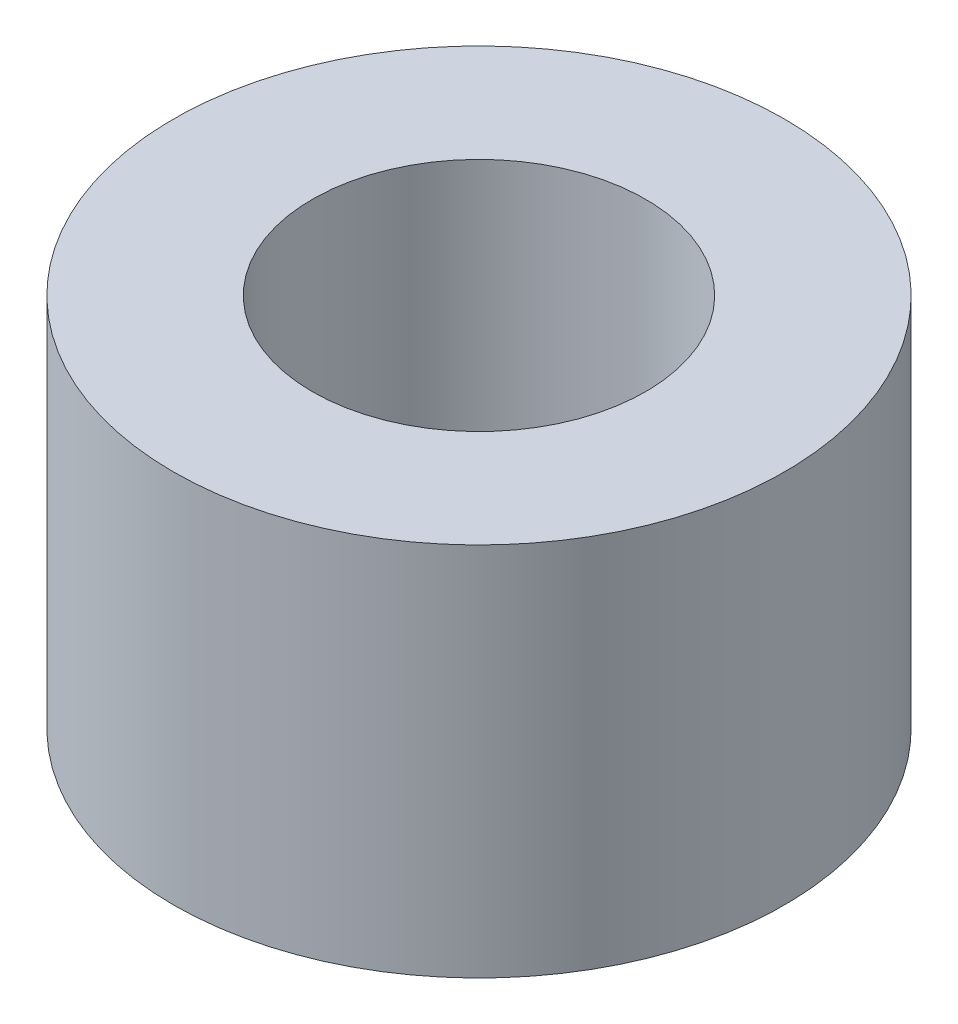
SolidWorks part; units mm, degrees
ref_plane "Front Plane" through (0, 0, 0) normal (0, 0, 1) x (1, 0, 0)
ref_plane "Top Plane" through (0, 0, 0) normal (0, 1, 0) x (1, 0, 0)
ref_plane "Right Plane" through (0, 0, 0) normal (1, 0, 0) x (0, 0, -1)
sketch "Sketch1" plane through (0, 0, 0) normal (0, 1, 0) x (1, 0, 0)
  circle A0 centre (0, 0) radius 3
  circle A1 centre (0, 0) radius 5.5
  dimension "D1" = 6
  dimension "D2" = 11
extrude "Boss-Extrude1" add sketch "Sketch1" along normal blind 6.75
